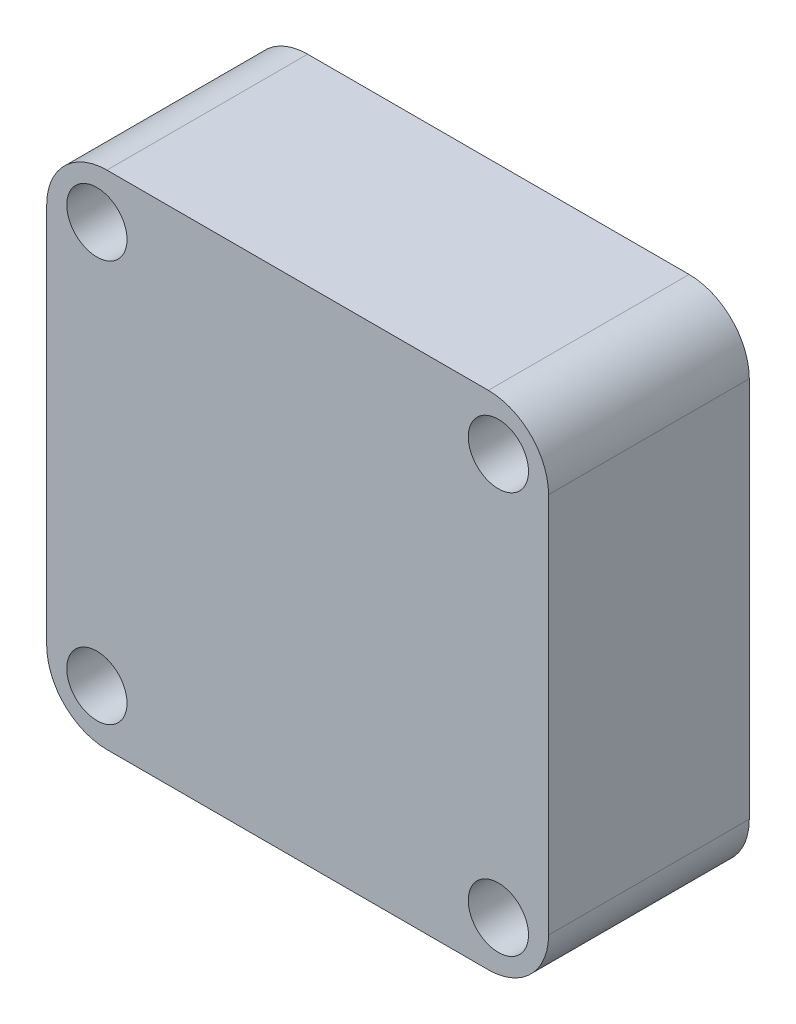
SolidWorks part; units mm, degrees
ref_plane "Front plane" through (0, 0, 0) normal (0, 0, 1) x (1, 0, 0)
ref_plane "Top plane" through (0, 0, 0) normal (0, 1, 0) x (1, 0, 0)
ref_plane "Right plane" through (0, 0, 0) normal (1, 0, 0) x (0, 0, -1)
sketch "Sketch1" plane through (0, 0, 0) normal (0, 0, 1) x (1, 0, 0)
  line L4 (-10, -110) -> (10, -130) construction
  line L5 (-9.5, -107.5) -> (9.5, -107.5)
  line L6 (-12.5, -110.5) -> (-12.5, -129.5)
  line L7 (-9.5, -132.5) -> (9.5, -132.5)
  line L8 (12.5, -110.5) -> (12.5, -129.5)
  line L9 (-12.5, -107.5) -> (12.5, -132.5) construction
  line L10 (-12.5, -132.5) -> (12.5, -107.5) construction
  arc A0 (-12.5, -129.5) -> (-9.5, -132.5) centre (-9.5, -129.5) ccw
  arc A1 (9.5, -132.5) -> (12.5, -129.5) centre (9.5, -129.5) ccw
  arc A2 (9.5, -107.5) -> (12.5, -110.5) centre (9.5, -110.5) cw
  arc A3 (-9.5, -107.5) -> (-12.5, -110.5) centre (-9.5, -110.5) ccw
  circle A4 centre (10, -130) radius 1.5 construction
  circle A5 centre (10, -110) radius 1.5 construction
  circle A6 centre (-10, -110) radius 1.5 construction
  circle A7 centre (-10, -130) radius 1.5 construction
  circle A8 centre (10, -130) radius 1.5
  circle A9 centre (10, -110) radius 1.5
  circle A10 centre (-10, -110) radius 1.5
  circle A11 centre (-10, -130) radius 1.5
  point P7 (0, -120)
  point P21 (0, -120)
  dimension "D3" = 3
  dimension "D1" = 25
  dimension "D2" = 25
extrude "Boss-Extrude1" add sketch "Sketch1" against normal blind 10
pattern_circular "CirPattern1" [suppressed] count 24 over 360
